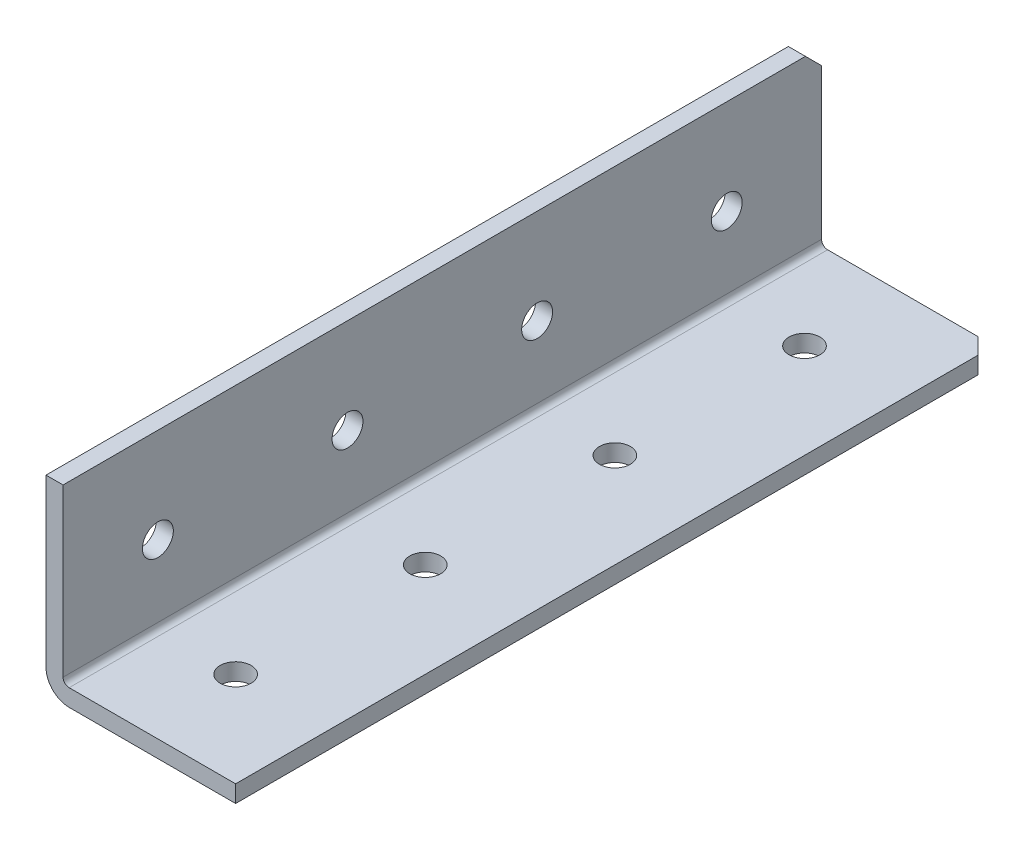
SolidWorks part; units mm, degrees
material "6061-T6 (SS)"
ref_plane "Front Plane" through (0, 0, 0) normal (0, 0, 1) x (1, 0, 0)
ref_plane "Top Plane" through (0, 0, 0) normal (0, 1, 0) x (1, 0, 0)
ref_plane "Right Plane" through (0, 0, 0) normal (1, 0, 0) x (0, 0, -1)
ref_plane "Plane1" through (0, 0, 0) normal (-1, 0, 0) x (0, -1, 0)
sketch "Sketch1" plane through (0, 0, 0) normal (-1, 0, 0) x (0, -1, 0)
  line L0 (0, 749.3) -> (-25.4, 749.3)
  line L1 (-25.4, 749.3) -> (-25.4, -749.3)
  line L2 (-25.4, -749.3) -> (0, -749.3)
  line L3 (0, -749.3) -> (0, 749.3)
extrude "Boss-Extrude1" add sketch "Sketch1" against normal blind 25.4
sketch "Sketch2" plane through (0, 0, -749.3) normal (0, 0, -1) x (-1, 0, 0)
  line L0 (-25.4, 2.286) -> (-2.286, 2.286)
  line L1 (-2.286, 2.286) -> (-2.286, 25.4)
  line L2 (-2.286, 25.4) -> (-25.4, 25.4)
  line L3 (-25.4, 25.4) -> (-25.4, 2.286)
extrude "Cut-Extrude1" cut sketch "Sketch2" against normal through all
hole_wizard "M3.5 Clearance Hole1" positions "Sketch4" profile "Sketch3" hole size "M3.5" standard "ANSI Metric"
sketch "Sketch4" plane through (0, 0, 0) normal (0, -1, 0) x (-1, 0, 0)
  point P0 (-12.7, 736.6)
  point P1 (-12.7, 711.2)
  point P2 (-12.7, 685.8)
  point P3 (-12.7, 660.4)
  point P4 (-12.7, 635)
  point P5 (-12.7, 609.6)
  point P6 (-12.7, 584.2)
  point P7 (-12.7, 558.8)
  point P8 (-12.7, 533.4)
  point P9 (-12.7, 508)
  point P10 (-12.7, 482.6)
  point P11 (-12.7, 457.2)
  point P12 (-12.7, 431.8)
  point P13 (-12.7, 406.4)
  point P14 (-12.7, 381)
  point P15 (-12.7, 355.6)
  point P16 (-12.7, 330.2)
  point P17 (-12.7, 304.8)
  point P18 (-12.7, 279.4)
  point P19 (-12.7, 254)
  point P20 (-12.7, 228.6)
  point P21 (-12.7, 203.2)
  point P22 (-12.7, 177.8)
  point P23 (-12.7, 152.4)
  point P24 (-12.7, 127)
  point P25 (-12.7, 101.6)
  point P26 (-12.7, 76.2)
  point P27 (-12.7, 50.8)
  point P28 (-12.7, 25.4)
  point P29 (-12.7, 0)
  point P30 (-12.7, -25.4)
  point P31 (-12.7, -50.8)
  point P32 (-12.7, -76.2)
  point P33 (-12.7, -101.6)
  point P34 (-12.7, -127)
  point P35 (-12.7, -152.4)
  point P36 (-12.7, -177.8)
  point P37 (-12.7, -203.2)
  point P38 (-12.7, -228.6)
  point P39 (-12.7, -254)
  point P40 (-12.7, -279.4)
  point P41 (-12.7, -304.8)
  point P42 (-12.7, -330.2)
  point P43 (-12.7, -355.6)
  point P44 (-12.7, -381)
  point P45 (-12.7, -406.4)
  point P46 (-12.7, -431.8)
  point P47 (-12.7, -457.2)
  point P48 (-12.7, -482.6)
  point P49 (-12.7, -508)
  point P50 (-12.7, -533.4)
  point P51 (-12.7, -558.8)
  point P52 (-12.7, -584.2)
  point P53 (-12.7, -609.6)
  point P54 (-12.7, -635)
  point P55 (-12.7, -660.4)
  point P56 (-12.7, -685.8)
  point P57 (-12.7, -711.2)
  point P58 (-12.7, -736.6)
sketch "Sketch3" plane through (12.7, 0, -736.6) normal (1, 0, 0) x (0, 0, -1)
  line L0 (0, 0) -> (0, 25.4)
  line L1 (0, 25.4) -> (2.0701, 25.4)
  line L2 (2.0701, 25.4) -> (2.0701, 0)
  line L5 (2.0701, 0) -> (0, 0)
  line L11 (0, -6.35) -> (0, 107.95) construction
  dimension "Thru Hole Dia." = 4.1402
  dimension "Thru Hole Depth" = 25.4
hole_wizard "M3.5 Clearance Hole2" positions "Sketch6" profile "Sketch5" hole size "M3.5" standard "ANSI Metric"
sketch "Sketch6" plane through (0, 0, 0) normal (-1, 0, 0) x (0, 0, 1)
  point P0 (711.2, 12.7)
  point P1 (736.6, 12.7)
  point P2 (685.8, 12.7)
  point P3 (660.4, 12.7)
  point P4 (635, 12.7)
  point P5 (609.6, 12.7)
  point P6 (584.2, 12.7)
  point P7 (558.8, 12.7)
  point P8 (533.4, 12.7)
  point P9 (508, 12.7)
  point P10 (482.6, 12.7)
  point P11 (457.2, 12.7)
  point P12 (431.8, 12.7)
  point P13 (406.4, 12.7)
  point P14 (381, 12.7)
  point P15 (355.6, 12.7)
  point P16 (330.2, 12.7)
  point P17 (304.8, 12.7)
  point P18 (279.4, 12.7)
  point P19 (254, 12.7)
  point P20 (228.6, 12.7)
  point P21 (203.2, 12.7)
  point P22 (177.8, 12.7)
  point P23 (152.4, 12.7)
  point P24 (127, 12.7)
  point P25 (101.6, 12.7)
  point P26 (76.2, 12.7)
  point P27 (50.8, 12.7)
  point P28 (25.4, 12.7)
  point P29 (0, 12.7)
  point P30 (-25.4, 12.7)
  point P31 (-50.8, 12.7)
  point P32 (-76.2, 12.7)
  point P33 (-101.6, 12.7)
  point P34 (-127, 12.7)
  point P35 (-152.4, 12.7)
  point P36 (-177.8, 12.7)
  point P37 (-203.2, 12.7)
  point P38 (-228.6, 12.7)
  point P39 (-254, 12.7)
  point P40 (-279.4, 12.7)
  point P41 (-304.8, 12.7)
  point P42 (-330.2, 12.7)
  point P43 (-355.6, 12.7)
  point P44 (-381, 12.7)
  point P45 (-406.4, 12.7)
  point P46 (-431.8, 12.7)
  point P47 (-457.2, 12.7)
  point P48 (-482.6, 12.7)
  point P49 (-508, 12.7)
  point P50 (-533.4, 12.7)
  point P51 (-558.8, 12.7)
  point P52 (-584.2, 12.7)
  point P53 (-609.6, 12.7)
  point P54 (-635, 12.7)
  point P55 (-660.4, 12.7)
  point P56 (-685.8, 12.7)
  point P57 (-711.2, 12.7)
  point P58 (-736.6, 12.7)
sketch "Sketch5" plane through (0, 12.7, 711.2) normal (0, 1, 0) x (0, 0, 1)
  line L0 (0, 0) -> (0, 25.4)
  line L1 (0, 25.4) -> (2.0701, 25.4)
  line L2 (2.0701, 25.4) -> (2.0701, 0)
  line L5 (2.0701, 0) -> (0, 0)
  line L11 (0, -6.35) -> (0, 107.95) construction
  dimension "Thru Hole Dia." = 4.1402
  dimension "Thru Hole Depth" = 25.4
chamfer "Chamfer1" distance 2.159 angle 45 4 edges at (25.4, 1.143, -749.3) (1.143, 25.4, -749.3) (1.143, 25.4, 749.3) (25.4, 1.143, 749.3)
fillet "Fillet1" radius 0.8128 1 edges at (2.286, 2.286, 0)
fillet "Fillet2" radius 3.0988 1 edges at (0, 0, 0)
sketch "Sketch8" plane through (0, 0, 749.3) normal (0, 0, 1) x (1, 0, 0)
  line L1 (-45.6555, -36.5704) -> (50.2275, -36.5704)
  line L2 (-45.6555, -36.5704) -> (-45.6555, 42.768)
  line L3 (-45.6555, 42.768) -> (50.2275, 42.768)
  line L4 (50.2275, -36.5704) -> (50.2275, 42.768)
  line L5 (-45.6555, -36.5704) -> (50.2275, 42.768) construction
  line L6 (-45.6555, 42.768) -> (50.2275, -36.5704) construction
  point P0 (2.286, 3.0988)
extrude "Cut-Extrude3" cut sketch "Sketch8" against normal blind 1397
